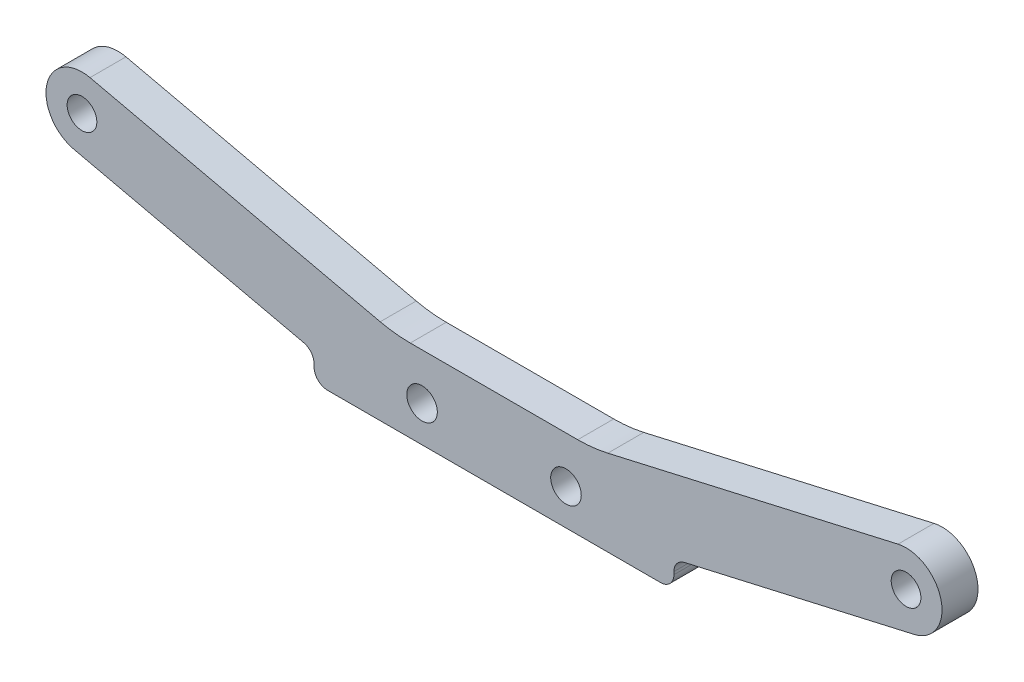
SolidWorks part; units mm, degrees
material "6061 Alloy"
ref_plane "Front Plane" through (0, 0, 0) normal (0, 0, 1) x (1, 0, 0)
ref_plane "Top Plane" through (0, 0, 0) normal (0, 1, 0) x (1, 0, 0)
ref_plane "Right Plane" through (0, 0, 0) normal (1, 0, 0) x (0, 0, -1)
sketch "Sketch2" plane through (0, 0, 0) normal (0, 0, 1) x (1, 0, 0)
  line L0 (-18.5, 0) -> (18.5, 0)
  line L1 (44.9087, 16.8994) -> (12.6498, 9.5263)
  line L2 (20, 1.8042) -> (20, 1.5)
  line L3 (46.6913, 9.1006) -> (21.1658, 3.2665)
  line L4 (0, 20.886) -> (0, -10.8572) construction
  line L5 (-46.6913, 9.1006) -> (-21.1658, 3.2665)
  line L6 (-20, 1.8042) -> (-20, 1.5)
  line L7 (-44.9087, 16.8994) -> (-12.6498, 9.5263)
  line L8 (-9.3076, 9.1493) -> (9.3076, 9.1493)
  circle A0 centre (-45.8, 13) radius 0.5
  circle A1 centre (-8, 4) radius 0.5
  arc A2 (-44.9087, 16.8994) -> (-46.6913, 9.1006) centre (-45.8, 13) ccw
  arc A3 (-12.6498, 9.5263) -> (-9.3076, 9.1493) centre (-9.3076, 24.1493) ccw
  arc A4 (-21.1658, 3.2665) -> (-20, 1.8042) centre (-21.5, 1.8042) cw
  arc A5 (21.1658, 3.2665) -> (20, 1.8042) centre (21.5, 1.8042) ccw
  arc A6 (12.6498, 9.5263) -> (9.3076, 9.1493) centre (9.3076, 24.1493) cw
  arc A7 (44.9087, 16.8994) -> (46.6913, 9.1006) centre (45.8, 13) cw
  circle A8 centre (8, 4) radius 0.5
  circle A9 centre (45.8, 13) radius 0.5
  arc A10 (20, 1.5) -> (18.5, 0) centre (18.5, 1.5) cw
  arc A11 (-20, 1.5) -> (-18.5, 0) centre (-18.5, 1.5) ccw
  point P3 (20, 3)
  point P20 (-11, 9.1493)
  point P23 (-20, 3)
  point P31 (0, 9.1493)
  point P33 (0, 0)
  point P34 (11, 9.1493)
  point P37 (20, 0)
  point P40 (-20, 0)
  dimension "D6" = 1.5
  dimension "D3" = 45.8
  dimension "D5" = 8
  dimension "D7" = 1
  dimension "D8" = 1
  dimension "D12" = 15
  dimension "D13" = 1.5
  dimension "D14" = 4
  dimension "D2" = 13
  dimension "D4" = 4
  dimension "D9" = 3
  dimension "D10" = 20
  dimension "D11" = 11
extrude "Base" add sketch "Sketch2" along normal mid plane 4
hole_wizard "M3 Clearance Hole1" positions "Sketch5" profile "Sketch6" hole size "M3" standard "ANSI Metric" end condition through all
sketch "Sketch5" plane through (0, 4, 2) normal (0, 0, 1) x (1, 0, 0)
  line L5 (-18.5, -4) -> (18.5, -4) construction
  line L6 (0, 1.3669) -> (0, -6.7301) construction
  point P0 (-8, 0)
  point P2 (8, 0)
  point P48 (0, 0)
  dimension "D1" = 16
  dimension "D2" = 4
  dimension "D3" = 8
sketch "Sketch6" plane through (-8, 4, 2) normal (1, 0, 0) x (0, -1, 0)
  line L0 (0, 0) -> (0, 4)
  line L1 (0, 4) -> (1.7, 4)
  line L2 (1.7, 4) -> (1.7, 0)
  line L5 (1.7, 0) -> (0, 0)
  line L11 (0, -6.35) -> (0, 107.95) construction
  dimension "Thru Hole Dia." = 3.4
  dimension "Thru Hole Depth" = 4
hole_wizard "M4x0.7 Tapped Hole1" positions "Sketch7" profile "Sketch8" tap size "M4x0.7" standard "ANSI Metric" end condition through all
sketch "Sketch7" plane through (0, 0, 2) normal (0, 0, -1) x (-1, 0, 0)
  line L5 (18.5, 0) -> (-18.5, 0) construction
  point P0 (-45.8, 13)
  point P2 (45.8, 13)
  dimension "D1" = 91.6
  dimension "D2" = 45.8
  dimension "D3" = 13
sketch "Sketch8" plane through (45.8, 13, 2) normal (1, 0, 0) x (0, -1, 0)
  line L0 (0, 0) -> (0, 4)
  line L1 (0, 4) -> (1.65, 4)
  line L2 (1.65, 4) -> (1.65, 0)
  line L5 (1.65, 0) -> (0, 0)
  line L11 (0, -6.35) -> (0, 107.95) construction
  dimension "Thread Major Dia." = 3.3
  dimension "Thru Tap Drill Depth" = 4
